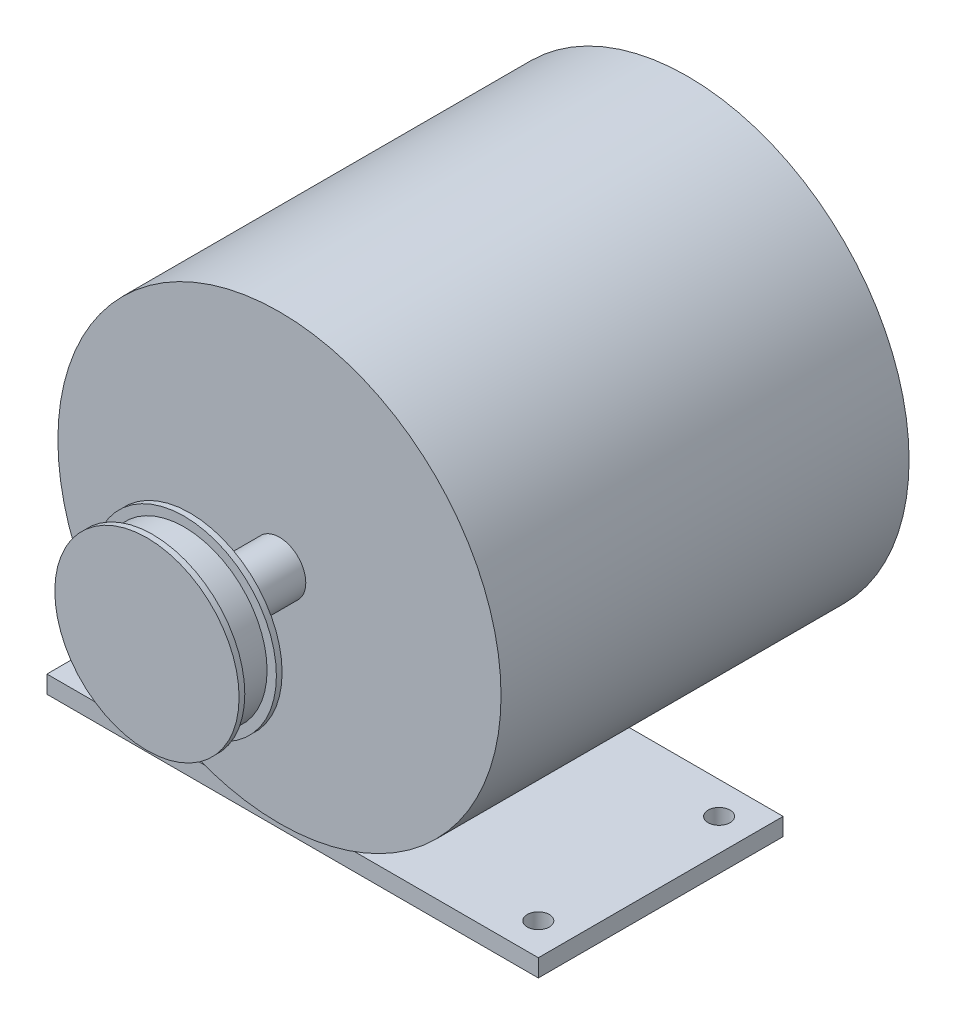
SolidWorks part; units mm, degrees
ref_plane "Front Plane" through (0, 0, 0) normal (0, 0, 1) x (1, 0, 0)
ref_plane "Top Plane" through (0, 0, 0) normal (0, 1, 0) x (1, 0, 0)
ref_plane "Right Plane" through (0, 0, 0) normal (1, 0, 0) x (0, 0, -1)
sketch "Sketch1" plane through (0, 0, 0) normal (0, 0, 1) x (1, 0, 0)
  circle A0 centre (0, 0) radius 50.5
  dimension "D1" = 101
extrude "Boss-Extrude1" add sketch "Sketch1" along normal blind 93
sketch "Sketch2" plane through (0, 0, 93) normal (0, 0, 1) x (1, 0, 0)
  circle A0 centre (0, 0) radius 6
  dimension "D1" = 12
extrude "Boss-Extrude2" add sketch "Sketch2" along normal blind 30.2
sketch "Sketch3" plane through (0, 0, 123.2) normal (0, 0, 1) x (1, 0, 0)
  circle A0 centre (0, 0) radius 21
extrude "Boss-Extrude3" add sketch "Sketch3" against normal blind 1.3
sketch "Sketch4" plane through (0, 0, 121.9) normal (0, 0, -1) x (-1, 0, 0)
  circle A0 centre (0, 0) radius 18.875
  dimension "D1" = 37.75
extrude "Boss-Extrude4" add sketch "Sketch4" along normal blind 7.2
sketch "Sketch5" plane through (0, 0, 114.7) normal (0, 0, -1) x (-1, 0, 0)
  circle A0 centre (0, 0) radius 21
  dimension "D1" = 42
extrude "Boss-Extrude5" add sketch "Sketch5" along normal blind 1.3
sketch "Sketch6" plane through (0, 0, 113.4) normal (0, 0, -1) x (-1, 0, 0)
  circle A0 centre (0, 0) radius 12.5
  dimension "D1" = 25
extrude "Boss-Extrude6" add sketch "Sketch6" along normal blind 5.6
ref_plane "Plane1" through (0, -54.5, 0) normal (0, 1, 0) x (1, 0, 0)
sketch "Sketch9" plane through (0, -54.5, 0) normal (0, 1, 0) x (1, 0, 0)
  line L0 (0, 0) -> (0, -93) construction
  line L1 (-50.5, -93) -> (50.5, -93) construction
  line L3 (-56, -34.2) -> (56, -34.2)
  line L4 (-56, -34.2) -> (-56, -90)
  line L5 (-56, -90) -> (56, -90)
  line L6 (56, -34.2) -> (56, -90)
  line L7 (-56, -34.2) -> (56, -90) construction
  line L8 (-56, -90) -> (56, -34.2) construction
  point P5 (-5.2912, -59.4638)
  dimension "D1" = 112
  dimension "D2" = 55.8
  dimension "D3" = 3
extrude "Boss-Extrude7" add sketch "Sketch9" along normal blind 4 separate body
sketch "Sketch10" plane through (0, -54.5, 0) normal (0, -1, 0) x (1, 0, 0)
  line L0 (-56, 90) -> (56, 90) construction
  line L1 (56, 90) -> (56, 34.2) construction
  line L2 (56, 34.2) -> (-56, 34.2) construction
  line L3 (-56, 34.2) -> (-56, 90) construction
  circle A0 centre (48.7, 82.7) radius 2.5
  circle A1 centre (48.7, 41.5) radius 2.5
  circle A2 centre (-48.7, 82.7) radius 2.5
  circle A3 centre (-48.7, 41.5) radius 2.5
  dimension "D9" = 5
  dimension "D10" = 5
  dimension "D11" = 5
  dimension "D12" = 5
  dimension "D1" = 7.3
  dimension "D2" = 7.3
  dimension "D3" = 7.3
  dimension "D4" = 7.3
  dimension "D5" = 7.3
  dimension "D6" = 7.3
  dimension "D7" = 7.3
  dimension "D8" = 7.3
extrude "Cut-Extrude1" cut sketch "Sketch10" against normal up to next (4 mm away)
